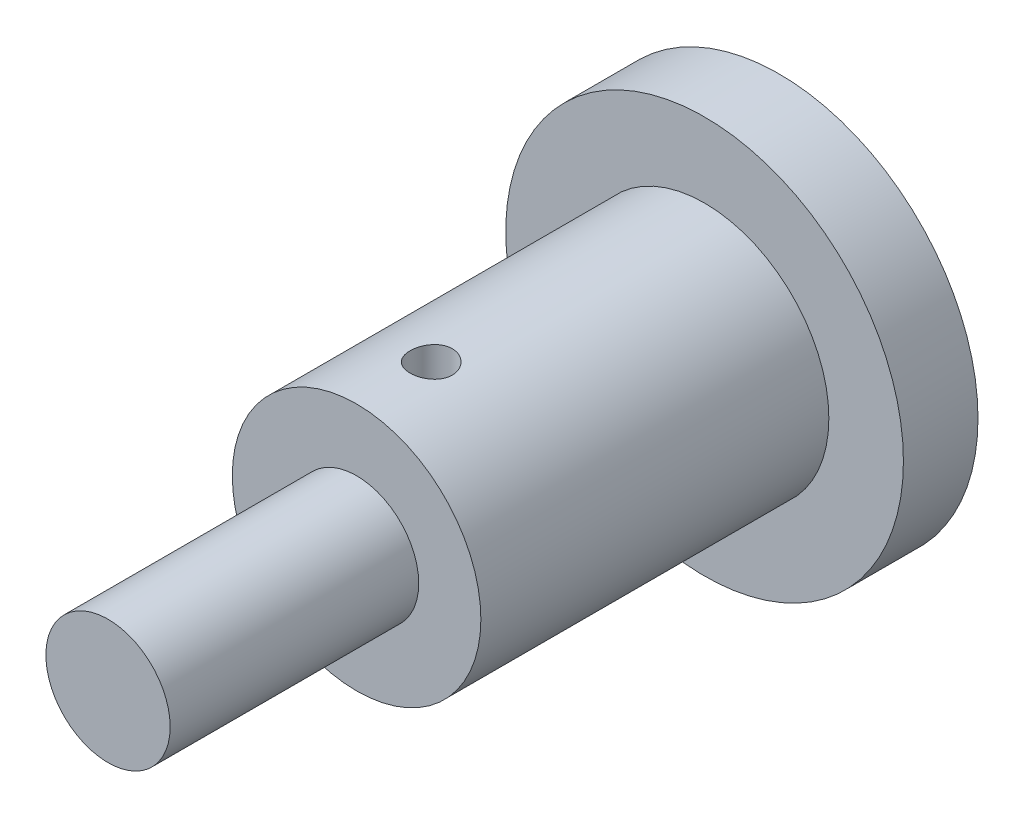
SolidWorks part; units mm, degrees
ref_plane "Front Plane" through (0, 0, 0) normal (0, 0, 1) x (1, 0, 0)
ref_plane "Top Plane" through (0, 0, 0) normal (0, 1, 0) x (1, 0, 0)
ref_plane "Right Plane" through (0, 0, 0) normal (1, 0, 0) x (0, 0, -1)
sketch "Sketch1" plane through (0, 0, 0) normal (0, 0, 1) x (1, 0, 0)
  circle A0 centre (0, 0) radius 8
  dimension "D1" = 16
extrude "Boss-Extrude1" add sketch "Sketch1" along normal blind 3
sketch "Sketch2" plane through (0, 0, 3) normal (0, 0, 1) x (1, 0, 0)
  circle A0 centre (0, 0) radius 5
  dimension "D1" = 10
extrude "Boss-Extrude2" add sketch "Sketch2" along normal blind 14
sketch "Sketch3" plane through (0, 0, 17) normal (0, 0, 1) x (1, 0, 0)
  circle A0 centre (0, 0) radius 2.5
  dimension "D1" = 5
extrude "Boss-Extrude3" add sketch "Sketch3" along normal blind 10
sketch "Sketch4" plane through (0, 0, 0) normal (0, 1, 0) x (1, 0, 0)
  line L0 (-5, -3) -> (-5, -17) construction
  circle A0 centre (0, -14) radius 0.85
  dimension "D2" = 1.7
  dimension "D1" = 5
  dimension "D3" = 14
extrude "Cut-Extrude1" cut sketch "Sketch4" against normal mid plane 15
